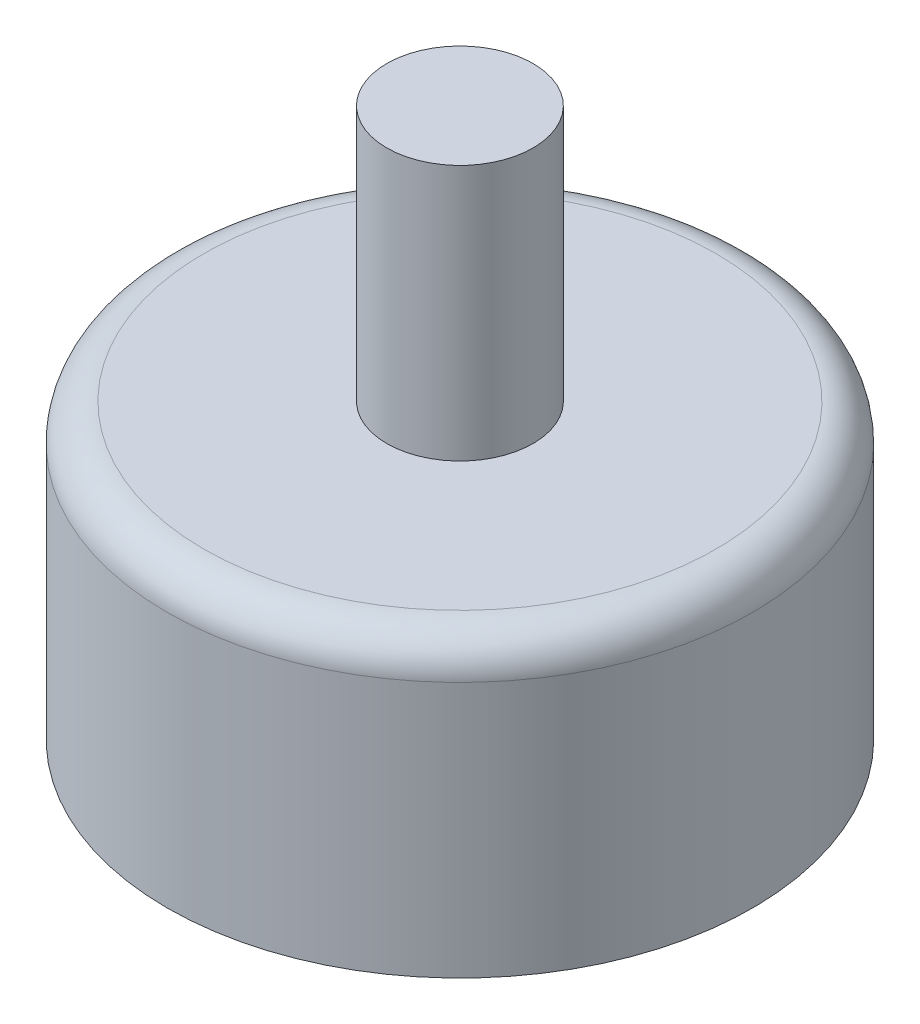
SolidWorks part; units mm, degrees
ref_plane "Front Plane" through (0, 0, 0) normal (0, 0, 1) x (1, 0, 0)
ref_plane "Top Plane" through (0, 0, 0) normal (0, 1, 0) x (1, 0, 0)
ref_plane "Right Plane" through (0, 0, 0) normal (1, 0, 0) x (0, 0, -1)
sketch "Sketch1" plane through (0, 0, 0) normal (0, 1, 0) x (1, 0, 0)
  circle A0 centre (0, 0) radius 20
  dimension "D1" = 40
extrude "Boss-Extrude1" add sketch "Sketch1" along normal blind 20
sketch "Sketch2" plane through (0, 20, 0) normal (0, 1, 0) x (1, 0, 0)
  circle A0 centre (0, 0) radius 5
  dimension "D1" = 10
extrude "Boss-Extrude2" add sketch "Sketch2" along normal blind 17.5
fillet "Fillet1" radius 2.5 1 edges at (0, 20, 20)
